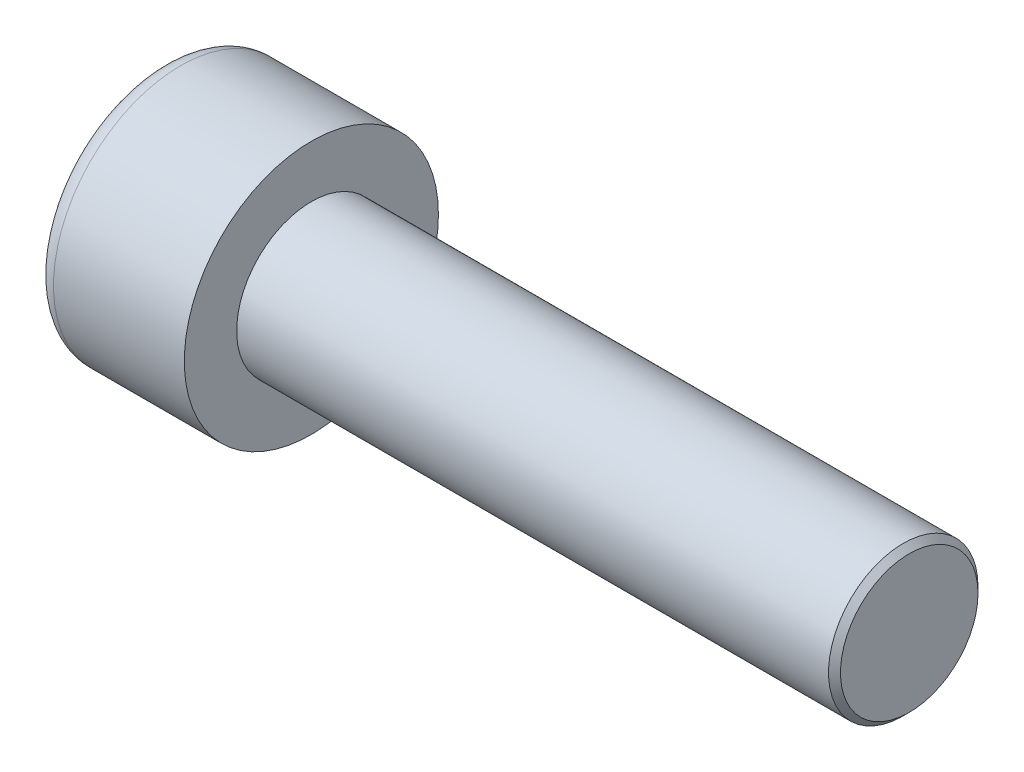
SolidWorks part; units mm, degrees
ref_plane "Front" through (0, 0, 0) normal (0, 0, 1) x (1, 0, 0)
ref_plane "Top" through (0, 0, 0) normal (0, 1, 0) x (1, 0, 0)
ref_plane "Right" through (0, 0, 0) normal (1, 0, 0) x (0, 0, -1)
sketch "Sketch1" plane through (0, 0, 0) normal (1, 0, 0) x (0, 0, -1)
  circle A0 centre (0, 0) radius 4.25
  dimension "dk" = 8.5
extrude "BaseHead" add sketch "Sketch1" along normal blind 5
sketch "Sketch2" plane through (5, 0, 0) normal (1, 0, 0) x (0, 0, -1)
  circle A0 centre (0, 0) radius 2.5
  dimension "d" = 5
extrude "BaseBody" add sketch "Sketch2" along normal blind 20
cosmetic thread "ThreadCosmetic1" parameters "b"=20, "D2"=4.134
sketch "Sketch3" plane through (0, 0, 0) normal (1, 0, 0) x (0, 0, -1)
  line L1 (2.3094, 0) -> (1.1547, 2)
  line L2 (1.1547, 2) -> (-1.1547, 2)
  line L3 (-1.1547, 2) -> (-2.3094, 0)
  line L4 (-2.3094, 0) -> (-1.1547, -2)
  line L5 (-1.1547, -2) -> (1.1547, -2)
  line L6 (1.1547, -2) -> (2.3094, 0)
  circle A0 centre (0, 0) radius 2 construction
  dimension "s" = 4
  dimension "e" = 4.6188
extrude "HexagonSocket" cut sketch "Sketch3" along normal blind 2.5
sketch "Sketch4" plane through (-4.1961, 0.75, 0) normal (0, 0, 1) x (-1, 0, 0)
  line L0 (-6.6961, 2.75) -> (-7.8508, 0.75)
  line L2 (-7.8508, 0.75) -> (-6.6961, 0.75)
  line L3 (-6.6961, 0.75) -> (-6.6961, 2.75)
  line L4 (-5.0351, 0.75) -> (0.839, 0.75) construction
  line L5 (-29.1961, 0.75) -> (-9.1961, 0.75) construction
  line L6 (-9.1961, 0.75) -> (-4.1961, 0.75) construction
  dimension "m" = 60
revolve "Cut-Revolve1" cut sketch "Sketch4" angle 360 about L4
fillet "HeadFillet" [suppressed] radius 0.2
fillet "TopFillet" radius 0.625 1 edges at (0, 0, -4.25)
chamfer "Chamfer1" distance 0.2 angle 45 1 edges at (25, 0, -2.5)
sketch "Sketch5" plane through (0, 0, 0) normal (0, 0, 1) x (1, 0, 0)
  line L0 (24.8, 2.125) -> (25.0165, 2.5)
  line L1 (25.0165, 2.5) -> (25.0165, 2.933)
  line L2 (25.0165, 2.933) -> (24.5835, 2.933)
  line L3 (24.5835, 2.933) -> (24.5835, 2.5)
  line L4 (24.5835, 2.5) -> (24.8, 2.125)
  line L5 (0, 0) -> (7.8886, 0) construction
  line L6 (24.8, -2.5) -> (24.8, 2.5) construction
  dimension "D1" = 5
  dimension "D2" = 0.433
revolve "Cut-Revolve10" [suppressed] cut sketch "Sketch5" angle 360 about L5
pattern_linear "LPattern10" [suppressed] count 38 spacing 0.5196 along (1, 0, 0)
equation "\"r1@TopFillet\" = \"d@Sketch2\" / 8"
equation "\"D1@Chamfer1\" = \"r@HeadFillet\""
equation "\"D1@Sketch5\" = \"d@Sketch2\""
equation "\"D2@Sketch5\" =  ( \"d@Sketch2\" - \"D2@ThreadCosmetic1\" )  / 2"
equation "\"D3@LPattern10\" = \"D2@Sketch5\" * 1.2"
equation "\"D1@LPattern10\" = \"b@ThreadCosmetic1\" / \"D3@LPattern10\""
